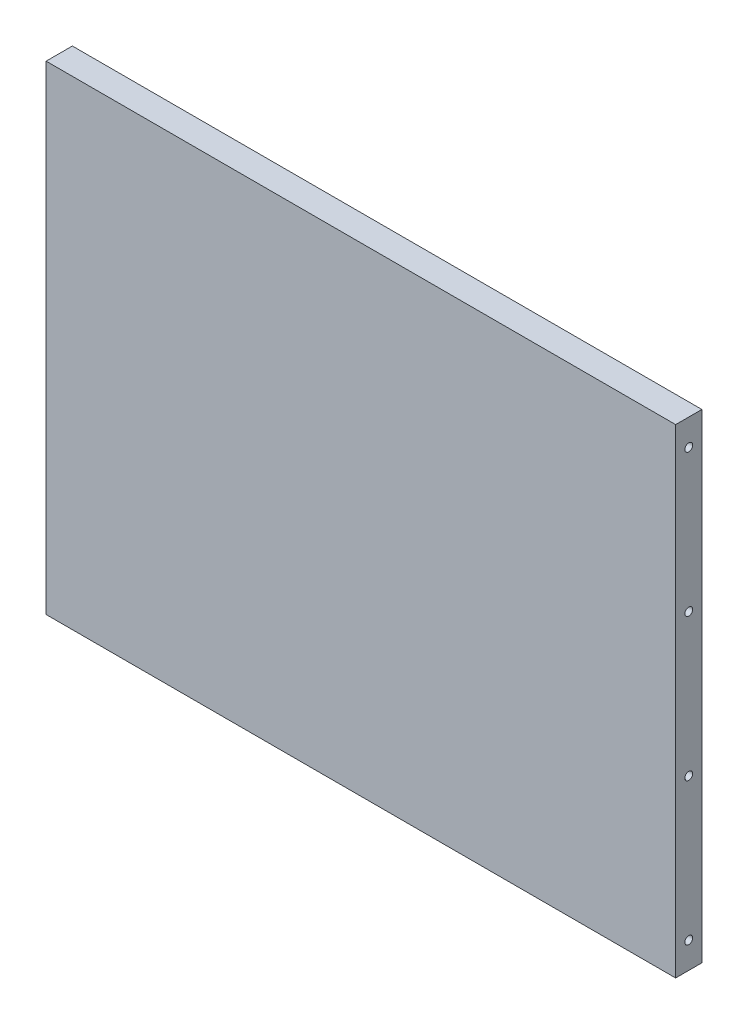
SolidWorks part; units mm, degrees
material "PC High Viscosity"
ref_plane "Front Plane" through (0, 0, 0) normal (0, 0, 1) x (1, 0, 0)
ref_plane "Top Plane" through (0, 0, 0) normal (0, 1, 0) x (1, 0, 0)
ref_plane "Right Plane" through (0, 0, 0) normal (1, 0, 0) x (0, 0, -1)
sketch "Sketch1" plane through (0, 0, 0) normal (0, 0, 1) x (1, 0, 0)
  line L1 (-152.4, -116.025) -> (152.4, -116.025)
  line L2 (-152.4, -116.025) -> (-152.4, 116.025)
  line L3 (-152.4, 116.025) -> (152.4, 116.025)
  line L4 (152.4, -116.025) -> (152.4, 116.025)
  point P5 (0, 116.025)
extrude "Boss-Extrude1" add sketch "Sketch1" against normal blind 12.7
hole_wizard "#10-24 Tapped Hole1" positions "Sketch2" profile "Sketch3" tap size "#10-24" standard "ANSI Inch"
sketch "Sketch2" plane through (-152.4, 0, 0) normal (-1, 0, 0) x (0, 0, 1)
  point P0 (-6.35, 103.325)
  point P3 (-6.35, 34.4417)
  point P6 (-6.35, -34.4417)
  point P9 (-6.35, -103.325)
sketch "Sketch3" plane through (-152.4, 103.325, -6.35) normal (0, 1, 0) x (0, 0, 1)
  line L0 (0, 0) -> (0, 20.1908)
  line L1 (0, 20.1908) -> (1.8986, 19.05)
  line L2 (1.8986, 19.05) -> (1.8986, 0)
  line L5 (1.8986, 0) -> (0, 0)
  line L10 (0, 20.1908) -> (-1.8986, 19.05) construction
  line L11 (0, -6.35) -> (0, 107.95) construction
  dimension "Tap Drill Dia." = 3.7973
  dimension "Tap Drill Depth" = 19.05
  dimension "Drill Angle" = 118
cosmetic thread "Hole Thread1" parameters "D1"=15.24, "D2"=4.826
cosmetic thread "Hole Thread2" parameters "D1"=15.24, "D2"=4.826
cosmetic thread "Hole Thread3" parameters "D1"=15.24, "D2"=4.826
cosmetic thread "Hole Thread4" parameters "D1"=15.24, "D2"=4.826
mirror "Mirror1" about plane through (0, 0, 0) normal (1, 0, 0) of "#10-24 Tapped Hole1"
cosmetic thread "Hole Thread5" parameters "D1"=15.24, "D2"=4.826
cosmetic thread "Hole Thread6" parameters "D1"=15.24, "D2"=4.826
cosmetic thread "Hole Thread7" parameters "D1"=15.24, "D2"=4.826
cosmetic thread "Hole Thread8" parameters "D1"=15.24, "D2"=4.826
